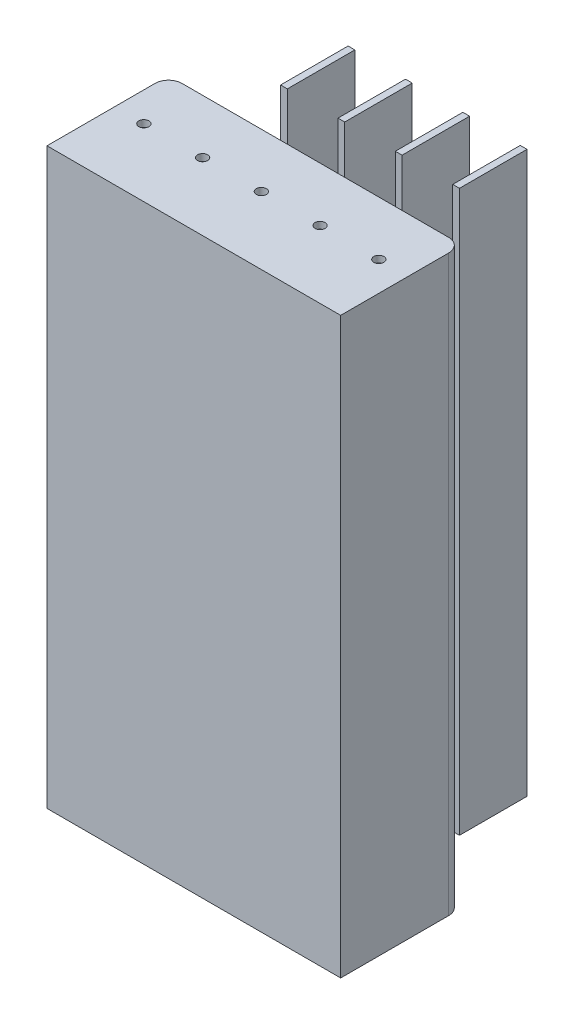
SolidWorks part; units mm, degrees
ref_plane "Front Plane" through (0, 0, 0) normal (0, 0, 1) x (1, 0, 0)
ref_plane "Top Plane" through (0, 0, 0) normal (0, 1, 0) x (1, 0, 0)
ref_plane "Right Plane" through (0, 0, 0) normal (1, 0, 0) x (0, 0, -1)
ref_plane "SPA Plane" through (0, 0, 5) normal (0, 0, 1) x (1, 0, 0)
sketch "Sketch1" plane through (0, 0, 5) normal (0, 0, 1) x (1, 0, 0)
  line L1 (173.8799, -109.5781) -> (260.8799, -109.5781)
  line L2 (173.8799, -109.5781) -> (173.8799, -279.5781)
  line L3 (173.8799, -279.5781) -> (260.8799, -279.5781)
  line L4 (260.8799, -109.5781) -> (260.8799, -279.5781)
  dimension "D1" = 170
  dimension "D2" = 87
extrude "Boss-Extrude1" add sketch "Sketch1" along normal blind 22
shell "Shell1" thickness 2
sketch "Sketch2" plane through (0, 0.0003, -36.1957) normal (0, 0, 1) x (1, 0, 0)
  line L0 (191.8799, -111.5779) -> (191.8799, -277.5779)
  line L1 (258.8799, -111.5779) -> (175.8799, -111.5779) construction
  line L2 (175.8799, -277.5779) -> (258.8799, -277.5779) construction
  line L3 (208.8799, -111.5779) -> (208.8799, -277.5779)
  line L4 (225.8799, -111.5779) -> (225.8799, -277.5779)
  line L5 (242.8799, -111.5779) -> (242.8799, -277.5779)
  line L6 (175.8799, -111.5779) -> (175.8799, -277.5779) construction
  line L7 (258.8799, -277.5779) -> (258.8799, -111.5779) construction
  line L8 (175.8799, -277.5779) -> (258.8799, -277.5779) construction
  dimension "D1" = 16
  dimension "D2" = 17
  dimension "D3" = 17
  dimension "D4" = 17
  dimension "D5" = 16
  dimension "D6" = 83
extrude "Extrude-Thin2" add sketch "Sketch2" along normal blind 20 thin thin type mid plane wall 2
sketch "Sketch3" plane through (0, -109.5781, 0) normal (0, 1, 0) x (1, 0, 0)
  line L0 (173.8799, -16) -> (260.8799, -16)
  line L1 (173.8799, -27) -> (173.8799, -5) construction
  line L2 (260.8799, -27) -> (260.8799, -5) construction
  point P12 (182.5799, -16)
  point P13 (199.9799, -16)
  point P14 (217.3799, -16)
  point P15 (234.7799, -16)
  point P16 (252.1799, -16)
  dimension "D1" = 8.7
  dimension "D3" = 17.4
  dimension "D4" = 17.4
  dimension "D5" = 17.4
  dimension "D6" = 8.7
  dimension "D7" = 17.4
hole_wizard "Ø3.0mm Dowel Hole1" positions "Sketch4" profile "Sketch5" hole size "Ø3.0" standard "BSI" end condition up to next
sketch "Sketch4" plane through (0, -109.5781, 0) normal (0, 1, 0) x (1, 0, 0)
  point P0 (182.5799, -16)
  point P3 (199.9799, -16)
  point P6 (217.3799, -16)
  point P9 (234.7799, -16)
  point P12 (252.1799, -16)
sketch "Sketch5" plane through (182.5799, -109.5781, 16) normal (1, 0, 0) x (0, 0, 1)
  line L0 (0, 0) -> (0, 2)
  line L1 (0, 2) -> (1.5, 2)
  line L2 (1.5, 2) -> (1.5, 0)
  line L5 (1.5, 0) -> (0, 0)
  line L11 (0, -6.35) -> (0, 107.95) construction
  dimension "Thru Hole Dia." = 3
  dimension "Thru Hole Depth" = 2
sketch "Sketch6" plane through (0, 0, 27) normal (0, 0, 1) x (1, 0, 0)
  line L1 (173.8799, -109.5781) -> (260.8799, -109.5781)
  line L2 (173.8799, -109.5781) -> (173.8799, -279.5781)
  line L3 (173.8799, -279.5781) -> (260.8799, -279.5781)
  line L4 (260.8799, -109.5781) -> (260.8799, -279.5781)
sketch "Sketch7" plane through (0, 0, 0) normal (0, 0, 1) x (1, 0, 0)
  line L1 (173.8799, -109.5781) -> (260.8799, -109.5781)
  line L2 (173.8799, -109.5781) -> (173.8799, -279.5781)
  line L3 (173.8799, -279.5781) -> (260.8799, -279.5781)
  line L4 (260.8799, -109.5781) -> (260.8799, -279.5781)
extrude "Boss-Extrude2" add sketch "Sketch7" along normal up to surface (5 mm away) up to face at (217.3799, -194.5781, 5)
fillet "Fillet1" radius 4 2 edges at (260.8799, -194.5781, 0) (173.8799, -194.5781, 0)
extrude "Boss-Extrude3" add sketch "Sketch6" along normal blind 9
